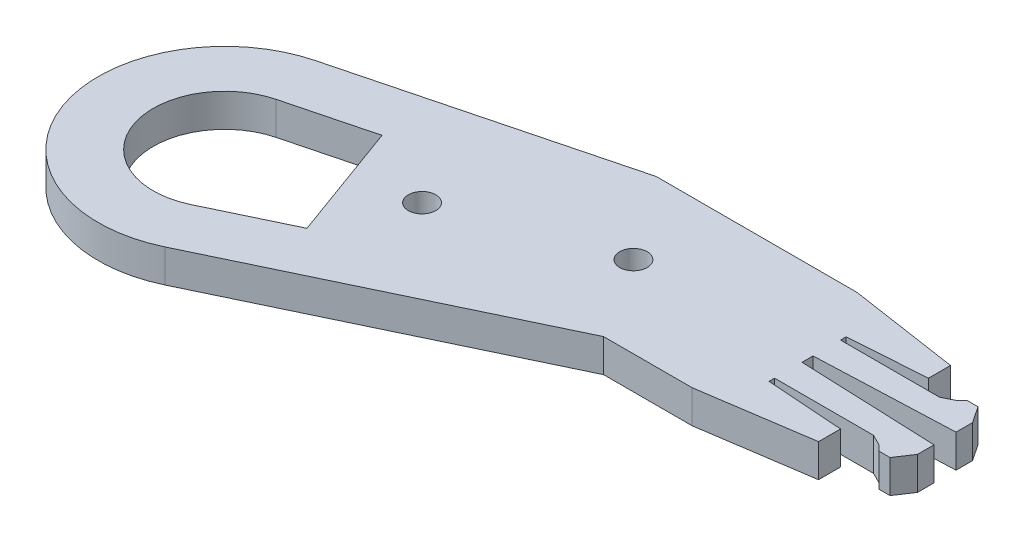
SolidWorks part; units mm, degrees
material "Lasercut ABS"
ref_plane "Front Plane" through (0, 0, 0) normal (0, 0, 1) x (1, 0, 0)
ref_plane "Top Plane" through (0, 0, 0) normal (0, 1, 0) x (1, 0, 0)
ref_plane "Right Plane" through (0, 0, 0) normal (1, 0, 0) x (0, 0, -1)
sketch "Sketch4" plane through (0, 0, 0) normal (0, 1, 0) x (1, 0, 0)
  line L0 (0, 0) -> (0, 17.2192) construction
  line L1 (-2.8794, 11.1337) -> (21.7373, 17.5)
  line L2 (4.9509, -10.3797) -> (31.9538, 2.5)
  line L3 (40, 2.5) -> (31.9538, 2.5)
  line L4 (40, 17.5) -> (21.7373, 17.5)
  arc A0 (-2.8794, 11.1337) -> (4.9509, -10.3797) centre (0, 0) ccw
  line B0 (6.0339, 8.2743) -> (9.9409, -2.46)
  line B1 (0, 0) -> (7.9874, 2.9072) construction
  line B2 (6.0339, 8.2743) -> (-1.6275, 6.293)
  line B3 (9.9409, -2.46) -> (2.7983, -5.8668)
  arc B4 (-1.6275, 6.293) -> (2.7983, -5.8668) centre (0, 0) ccw
  circle B5 centre (13.1557, 4.7883) radius 1.25
  circle B6 centre (27.2511, 9.9186) radius 1.25
  line B7 (40, 10) -> (43, 10) construction
  line B8 (43, 10.5) -> (43, 9.5)
  line B9 (43, 10.5) -> (55.5, 11)
  line B10 (55.5, 11) -> (55.5, 12.5)
  line B11 (55.5, 12.5) -> (54.5, 14)
  line B12 (54.5, 14) -> (53.5, 14)
  line B13 (53.5, 14) -> (53, 13.5)
  line B14 (53, 13.5) -> (52, 13)
  line B15 (52, 13) -> (43, 13)
  line B16 (43, 13) -> (43, 13.5)
  line B17 (43, 13.5) -> (50, 14)
  line B18 (50, 14) -> (50, 16)
  line B19 (50, 16) -> (40, 17.5)
  line B20 (43, 9.5) -> (55.5, 9)
  line B21 (55.5, 9) -> (55.5, 7.5)
  line B22 (55.5, 7.5) -> (54.5, 6)
  line B23 (54.5, 6) -> (53.5, 6)
  line B24 (53.5, 6) -> (53, 6.5)
  line B25 (53, 6.5) -> (52, 7)
  line B26 (52, 7) -> (43, 7)
  line B27 (43, 7) -> (43, 6.5)
  line B28 (43, 6.5) -> (50, 6)
  line B29 (50, 6) -> (50, 4)
  line B30 (50, 4) -> (40, 2.5)
  dimension "D1" = 70
  dimension "D2" = 5
  dimension "D3" = 10
  dimension "D4" = 50
sketch_block_instance "Block-Horn-TowerPro-1"
sketch_block "Block1" parameters "D1"=6.5, "D4"=2.5, "D2"=15, "D3"=11, "D5"=14, "D6"=15
sketch_block_instance "Block-Snap-Textile-1"
sketch_block "Block-Snap-Textile" parameters "D1"=3, "D2"=1, "D3"=2, "D4"=1.5, "D5"=10, "D6"=0.5, "D7"=9, "D8"=1, "D9"=0.5, "D10"=0.5, "D11"=0.5, "D12"=1, "D13"=12.5, "D14"=0.5, "D15"=0.5, "D16"=1.5, "D17"=1.5
extrude "Boss-Extrude2" add sketch "Sketch4" against normal blind 3 contours L0 A0 L2 L3 B30 B29 B28 B27 B26 B25 B24 B23 B22 B21 B20 B8 B9 B10 B11 B12 B13 B14 B15 B16 B17 B18 B19 L4 L1 B2 B0 B3 B4 B6 B5 | A0 L0 B4 B2 L1
sketch "Sketch5" plane through (0, 0, 0) normal (0, 1, 0) x (1, 0, 0)
  line L0 (5.5185, 9.6904) -> (21.0089, 13.6965) construction
  line L1 (11.3153, -6.2361) -> (25.7566, 0.652) construction
  line L2 (6.0339, 8.2743) -> (9.9409, -2.46) construction
  line L3 (-2.8794, 11.1337) -> (21.7373, 17.5) construction
  line L4 (4.9509, -10.3797) -> (31.9538, 2.5) construction
  text T0 "EB5" font "1CamBam_Stick_3" height 2.5
  text T1 "ONO V2" font "1CamBam_Stick_3" height 2.5
  dimension "D1" = 16
  dimension "D2" = 3.5
  dimension "D3" = 1
equation "\"X\"= 10"
equation "\"Y\"= 50"
equation "\"D3@Sketch4\"=\"X\""
equation "\"D4@Sketch4\"=\"Y\""
